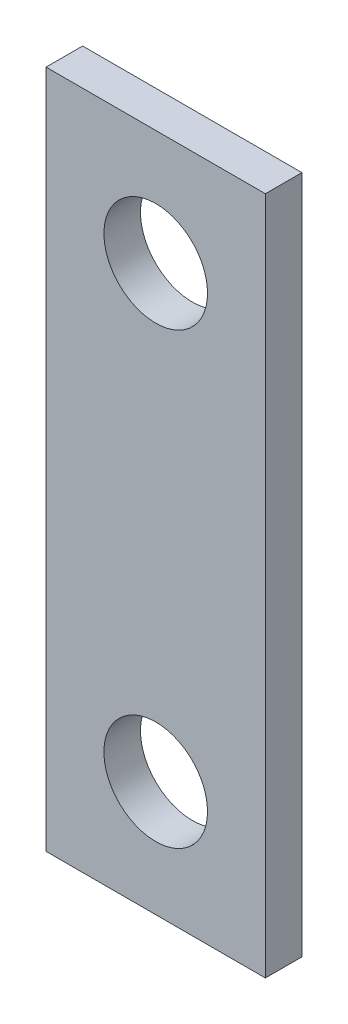
SolidWorks part; units mm, degrees
material "Copper"
ref_plane "Front Plane" through (0, 0, 0) normal (0, 0, 1) x (1, 0, 0)
ref_plane "Top Plane" through (0, 0, 0) normal (0, 1, 0) x (1, 0, 0)
ref_plane "Right Plane" through (0, 0, 0) normal (1, 0, 0) x (0, 0, -1)
sketch "Sketch1" plane through (0, 0, 0) normal (0, 0, 1) x (1, 0, 0)
  line L0 (17, 0) -> (17, -39) construction
  line L1 (8.1971, 10) -> (25.8029, 10) construction
  line L2 (7.475, 10) -> (26.525, 10)
  line L3 (7.475, 10) -> (7.475, -49)
  line L4 (7.475, -49) -> (26.525, -49)
  line L5 (26.525, 10) -> (26.525, -49)
  line L7 (8.1971, -49) -> (25.8029, -49) construction
  point P0 (17, 0)
  point P1 (17, -39)
  point P3 (17, -19.5)
  point P5 (17, -19.5)
  point P17 (17, 10)
  dimension "D1" = 19.05
extrude "Boss-Extrude1" add sketch "Sketch1" along normal blind 3.175 contours L5 L4 L3 L2
hole_wizard "Cell Module Terminal M8 Clearance Hole" positions "Sketch4" profile "Sketch3" hole size "M8" standard "ANSI Metric" end condition through all
sketch "Sketch4" plane through (0, 0, 3.175) normal (0, 0, 1) x (1, 0, 0)
  point P0 (17, 0)
  point P2 (17, -39)
sketch "Sketch3" plane through (17, 0, 3.175) normal (1, 0, 0) x (0, -1, 0)
  line L0 (0, 0) -> (0, 3.175)
  line L1 (0, 3.175) -> (4.5, 3.175)
  line L2 (4.5, 3.175) -> (4.5, 0)
  line L5 (4.5, 0) -> (0, 0)
  line L11 (0, -6.35) -> (0, 107.95) construction
  dimension "Thru Hole Dia." = 9
  dimension "Thru Hole Depth" = 3.175
hole_wizard "BMS #4-40 Tapped Hole" [suppressed] positions "Sketch5" profile "Sketch6" tap size "#4-40" standard "ANSI Inch"
sketch "Sketch5" plane through (0, 0, 0) normal (0, 0, -1) x (-1, 0, 0)
  point P0 (-17, -19.5)
sketch "Sketch6" plane through (17, -19.5, 0) normal (1, 0, 0) x (0, 1, 0)
  line L0 (0, 0) -> (0, 4.7625)
  line L1 (0, 4.7625) -> (1.1303, 4.7625)
  line L2 (1.1303, 4.7625) -> (1.1303, 0)
  line L5 (1.1303, 0) -> (0, 0)
  line L11 (0, -6.35) -> (0, 107.95) construction
  dimension "Thru Tap Drill Dia." = 2.2606
  dimension "Thru Tap Drill Depth" = 4.7625
cosmetic thread "Hole Thread1" [suppressed] parameters "D2"=2.8448
